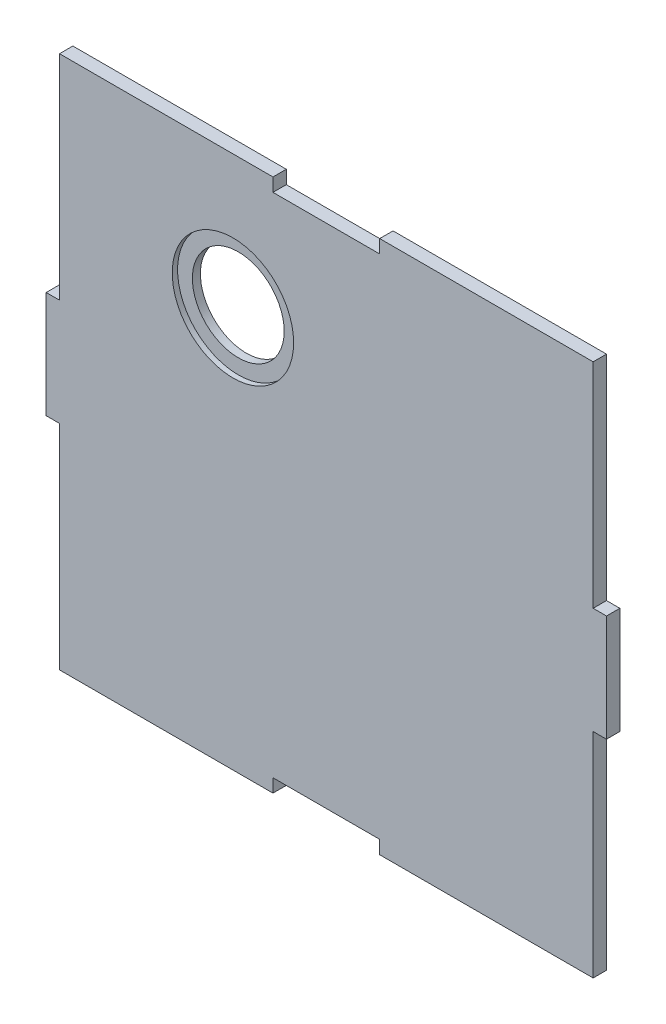
SolidWorks part; units mm, degrees
ref_plane "Alzado" through (0, 0, 0) normal (0, 0, 1) x (1, 0, 0)
ref_plane "Planta" through (0, 0, 0) normal (0, 1, 0) x (1, 0, 0)
ref_plane "Vista lateral" through (0, 0, 0) normal (1, 0, 0) x (0, 0, -1)
sketch "Croquis1" plane through (0, 0, 0) normal (0, 0, 1) x (1, 0, 0)
  line L0 (0, 0) -> (100, 0) construction
  line L2 (-100, -100) -> (-100, -20)
  line L3 (-100, 100) -> (-20, 100)
  line L5 (-100, -100) -> (100, 100) construction
  line L6 (-100, 100) -> (100, -100) construction
  line L8 (-20, 100) -> (-20, 95)
  line L9 (-20, 95) -> (20, 95)
  line L10 (20, 100) -> (20, 95)
  line L11 (20, 100) -> (100, 100)
  line L12 (20, -100) -> (100, -100)
  line L13 (20, -100) -> (20, -95)
  line L14 (-20, -95) -> (20, -95)
  line L15 (-20, -100) -> (-20, -95)
  line L16 (-100, -100) -> (-20, -100)
  line L17 (-100, 20) -> (-100, 100)
  line L18 (-100, 20) -> (-105, 20)
  line L20 (-100, -20) -> (-105, -20)
  line L21 (-105, 20) -> (-105, -20)
  line L22 (0, 0) -> (0, 42.2428) construction
  line L23 (105, 20) -> (105, -20)
  line L24 (100, -20) -> (105, -20)
  line L25 (100, 20) -> (105, 20)
  line L26 (100, 20) -> (100, 100)
  line L27 (100, -100) -> (100, -20)
  point P0 (0, 0)
  dimension "D1" = 200
  dimension "D2" = 200
  dimension "D3" = 5
  dimension "D4" = 40
  dimension "D5" = 5
  dimension "D6" = 40
extrude "Saliente-Extruir1" add sketch "Croquis1" along normal blind 5
sketch "Croquis2" plane through (0, 0, 5) normal (0, 0, 1) x (1, 0, 0)
  line L0 (105, 0) -> (40, 0) construction
  line L3 (105, -20) -> (105, 20) construction
  line L4 (-105, 20) -> (-105, -20) construction
  line L5 (-20, 100) -> (-100, 100) construction
  circle A0 centre (-35, 50) radius 17.2
  dimension "D1" = 34.4
  dimension "D2" = 65
  dimension "D3" = 70
  dimension "D4" = 50
extrude "Cortar-Extruir1" cut sketch "Croquis2" against normal up to vertex (5 mm away)
sketch "Croquis3" plane through (0, 0, 5) normal (0, 0, 1) x (1, 0, 0)
  circle A0 centre (-35, 50) radius 22.75
  dimension "D1" = 45.5
extrude "Cortar-Extruir2" cut sketch "Croquis3" against normal blind 2
